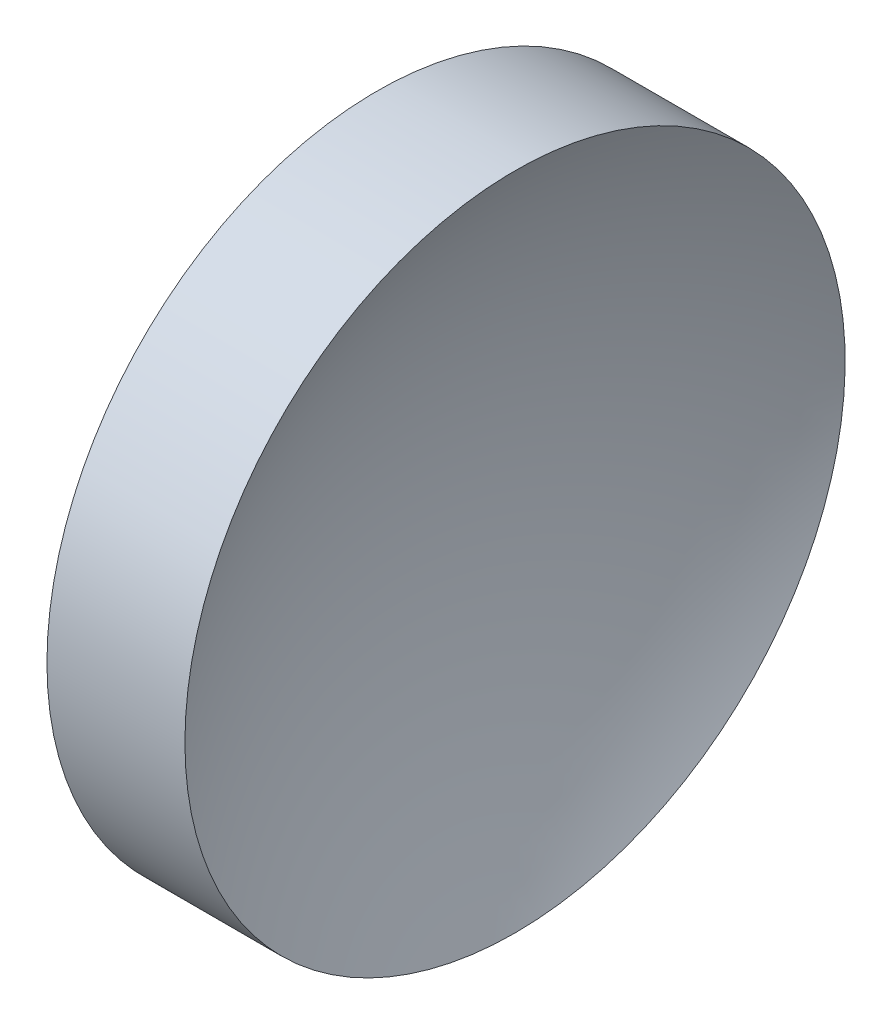
SolidWorks part; units mm, degrees
ref_plane "前视基准面" through (0, 0, 0) normal (0, 0, 1) x (1, 0, 0)
ref_plane "上视基准面" through (0, 0, 0) normal (0, 1, 0) x (1, 0, 0)
ref_plane "右视基准面" through (0, 0, 0) normal (1, 0, 0) x (0, 0, -1)
sketch "草图1" plane through (0, 0, 0) normal (0, 0, 1) x (1, 0, 0)
  line L0 (56.1009, 32.6108) -> (68.2773, 32.6108) construction
  line L1 (57.5323, 32.6108) -> (57.5323, 45.1108)
  line L2 (57.5323, 45.1108) -> (62.757, 45.1108)
  line L3 (59.5323, 32.6108) -> (57.5323, 32.6108)
  arc A0 (62.757, 45.1108) -> (59.5323, 32.6108) centre (85.3723, 32.6108) ccw
revolve "旋转1" add sketch "草图1" angle 360 about L0
